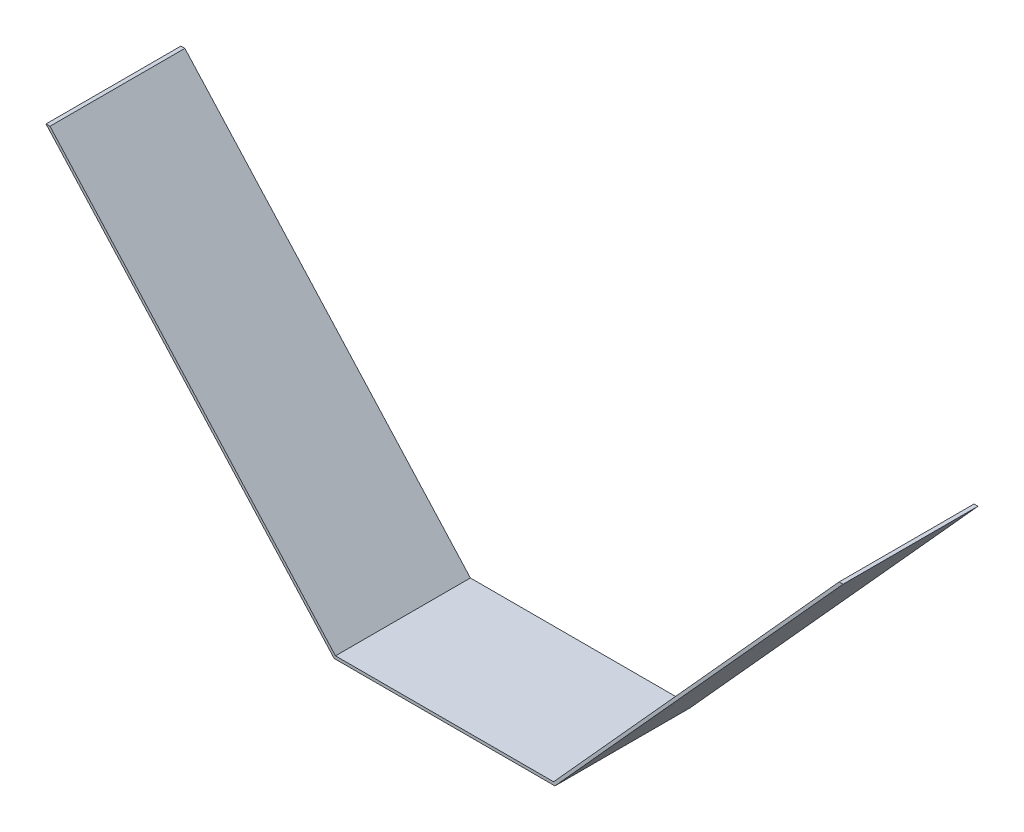
SolidWorks part; units mm, degrees
ref_plane "Front Plane" through (0, 0, 0) normal (0, 0, 1) x (1, 0, 0)
ref_plane "Top Plane" through (0, 0, 0) normal (0, 1, 0) x (1, 0, 0)
ref_plane "Right Plane" through (0, 0, 0) normal (1, 0, 0) x (0, 0, -1)
sketch "Sketch1" plane through (0, 0, 0) normal (0, 0, 1) x (1, 0, 0)
  line L0 (-374.7977, 95.5084) -> (37.9523, 95.5084)
  line L1 (-225.5727, -69.5916) -> (-111.2727, -69.5916)
  line L2 (-374.7977, 95.5084) -> (-225.5727, -69.5916)
  line L3 (-111.2727, -69.5916) -> (37.9523, 95.5084)
  point P7 (-168.4227, 95.5084)
  point P8 (-168.4227, -69.5916)
  dimension "D1" = 412.75
  dimension "D2" = 114.3
extrude "Boss-Extrude1" add sketch "Sketch1" along normal blind 69.85 contours L0 L3 L1 L2
shell "Shell10" thickness 1.524
